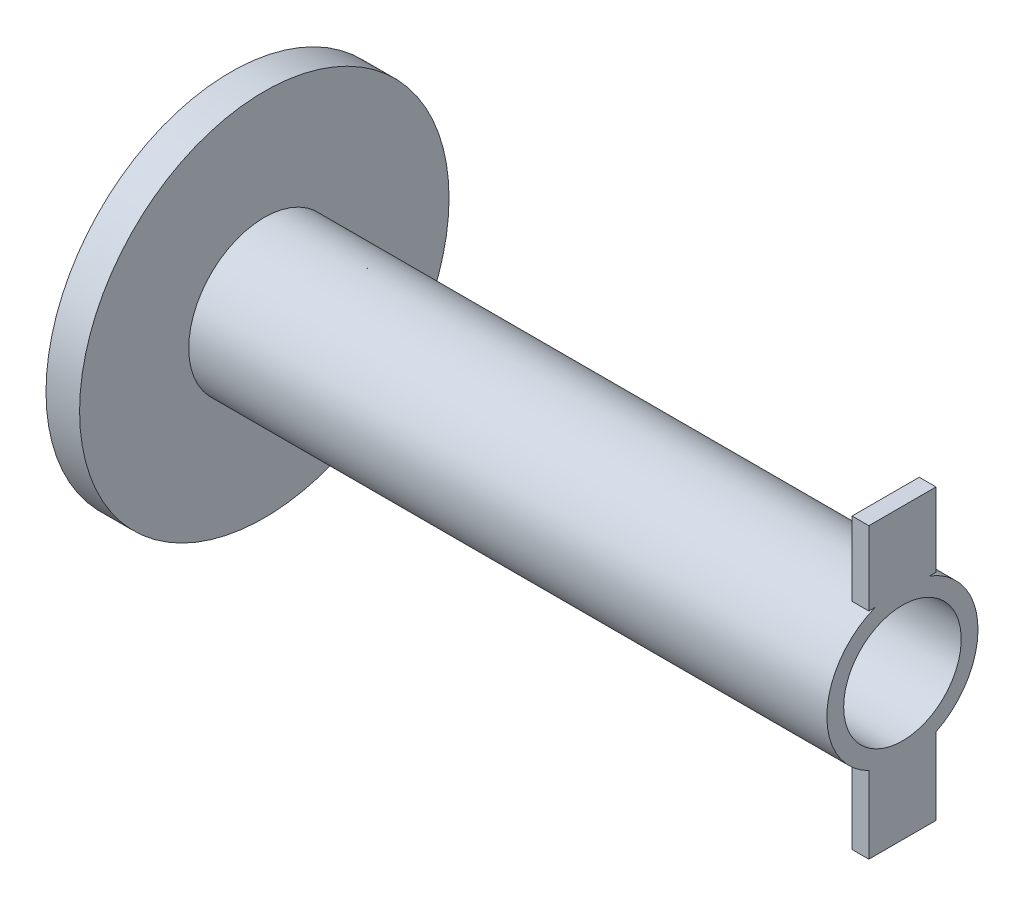
SolidWorks part; units mm, degrees
ref_plane "Front Plane" through (0, 0, 0) normal (0, 0, 1) x (1, 0, 0)
ref_plane "Top Plane" through (0, 0, 0) normal (0, 1, 0) x (1, 0, 0)
ref_plane "Right Plane" through (0, 0, 0) normal (1, 0, 0) x (0, 0, -1)
sketch "Sketch2" plane through (0, 0, 0) normal (1, 0, 0) x (0, 0, -1)
  circle A0 centre (0, 0) radius 55
extrude "Boss-Extrude1" add sketch "Sketch2" along normal blind 10
sketch "Sketch3" plane through (10, 0, 0) normal (1, 0, 0) x (0, 0, -1)
  circle A0 centre (0, 0) radius 22.5
extrude "Boss-Extrude2" add sketch "Sketch3" along normal blind 190
sketch "Sketch4" plane through (0, 0, 0) normal (-1, 0, 0) x (0, 0, 1)
  circle A0 centre (0, 0) radius 17.5
extrude "Cut-Extrude1" cut sketch "Sketch4" against normal through all both and the other way through all
sketch "Sketch9" plane through (200, 0, 0) normal (1, 0, 0) x (0, 0, -1)
  line L1 (-10, 43) -> (10, 43)
  line L2 (-10, 43) -> (-10, 21)
  line L3 (-10, 21) -> (10, 21)
  line L4 (10, 43) -> (10, 21)
  line L5 (-10, 43) -> (10, 21) construction
  line L6 (-10, 21) -> (10, 43) construction
  point P0 (0, 32)
extrude "Boss-Extrude3" add sketch "Sketch9" against normal blind 5
sketch "Sketch10" plane through (200, 0, 0) normal (1, 0, 0) x (0, 0, -1)
  line L1 (-10, -20) -> (10, -20)
  line L2 (-10, -20) -> (-10, -43)
  line L3 (-10, -43) -> (10, -43)
  line L4 (10, -20) -> (10, -43)
  line L5 (-10, -20) -> (10, -43) construction
  line L6 (-10, -43) -> (10, -20) construction
  point P0 (0, -31.5)
extrude "Boss-Extrude4" add sketch "Sketch10" against normal blind 5
